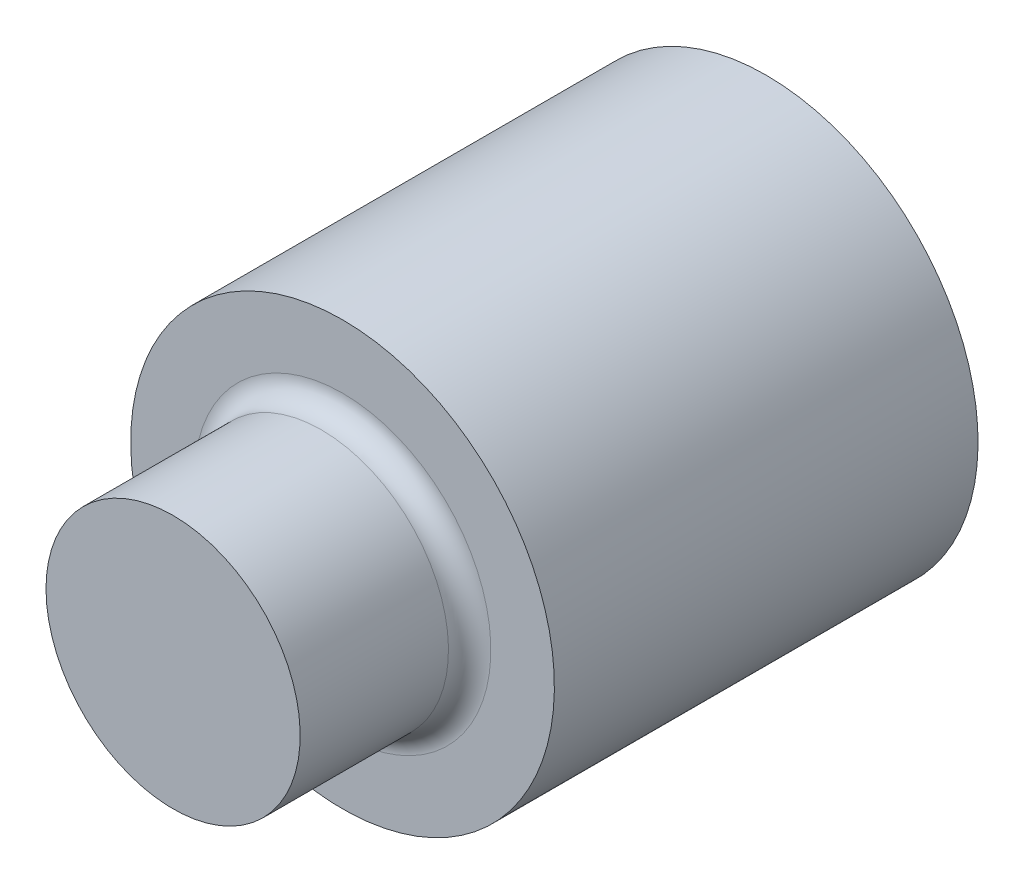
SolidWorks part; units mm, degrees
ref_plane "Front Plane" through (0, 0, 0) normal (0, 0, 1) x (1, 0, 0)
ref_plane "Top Plane" through (0, 0, 0) normal (0, 1, 0) x (1, 0, 0)
ref_plane "Right Plane" through (0, 0, 0) normal (1, 0, 0) x (0, 0, -1)
sketch "Sketch1" plane through (0, 0, 0) normal (1, 0, 0) x (0, 0, -1)
  line L0 (29, 0) -> (-29, 0) construction
  line L1 (29, 0) -> (34, 0) construction
  line L2 (-29, 1.5) -> (-29, -1.5) construction
  line L3 (34, 2.5) -> (34, -2.5) construction
  line L4 (34, 2.5) -> (29, 2.5) construction
  point P4 (0, 0)
  point P9 (-29, 0)
  point P12 (34, 0)
  dimension "Length" = 63
  dimension "Head Height" = 5
  dimension "Head Diameter" = 5
  dimension "Diameter" = 3
sketch "Sketch2" plane through (0, 0, 0) normal (1, 0, 0) x (0, 0, -1)
  line L0 (-29, 1.5) -> (28.75, 1.5)
  line L1 (29, 1.75) -> (29, 2.5)
  line L2 (29, 2.5) -> (34, 2.5)
  line L3 (34, 2.5) -> (34, 0)
  line L4 (34, 0) -> (-29, 0)
  line L5 (-29, 0) -> (-29, 1.5)
  arc A0 (28.75, 1.5) -> (29, 1.75) centre (28.75, 1.75) ccw
  dimension "D1" = 0.25
revolve "Revolve1" add sketch "Sketch2" angle 360 about L4
sketch "Sketch3" plane through (0, 0, 0) normal (1, 0, 0) x (0, 0, -1)
  line L0 (34, -2.5) -> (34, 2.5) construction
  line L1 (27, 2.6981) -> (-30.4593, 2.6981)
  line L2 (27, 2.6981) -> (27, -2.589)
  line L3 (27, -2.589) -> (-30.4593, -2.589)
  line L4 (-30.4593, 2.6981) -> (-30.4593, -2.589)
  line L5 (2.75, 0) -> (-2.75, 0) construction
  dimension "D1" = 7
  dimension "D2" = 5.2872
  dimension "D3" = 57.4593
  dimension "D4" = 2.6981
extrude "Cut-Extrude1" cut sketch "Sketch3" against normal through all and the other way through all
